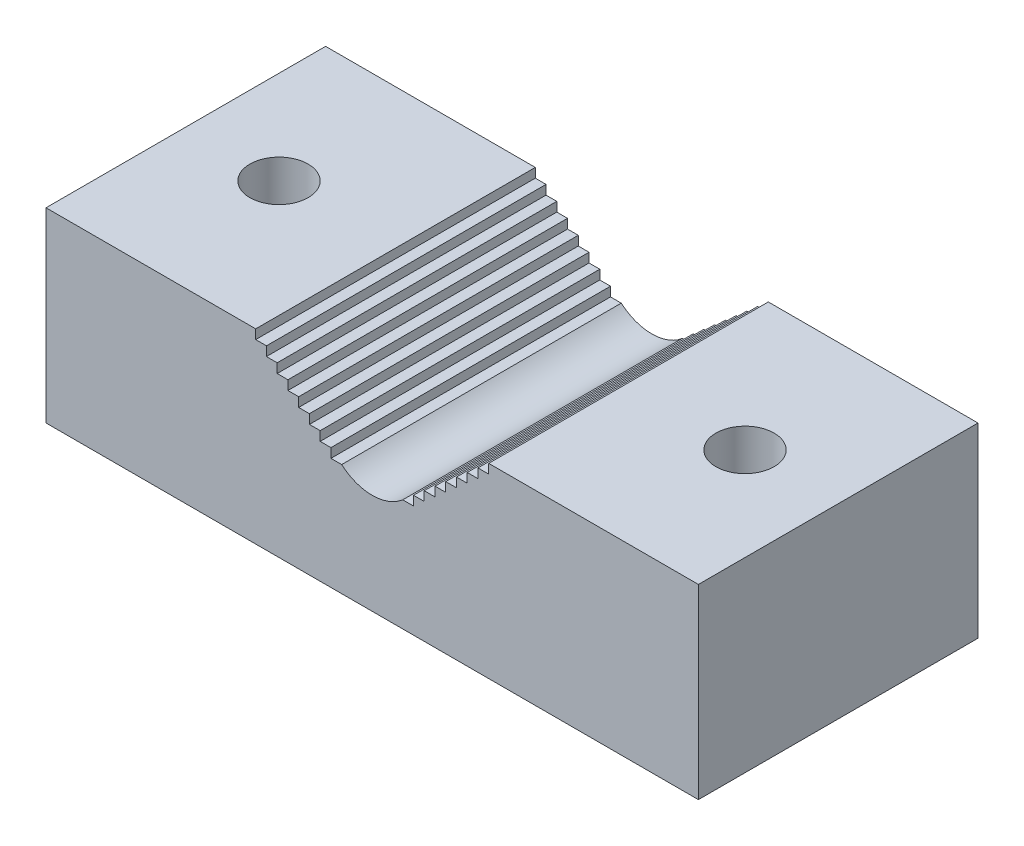
SolidWorks part; units mm, degrees
material "6061-T6 (SS)"
ref_plane "Front Plane" through (0, 0, 0) normal (0, 0, 1) x (1, 0, 0)
ref_plane "Top Plane" through (0, 0, 0) normal (0, 1, 0) x (1, 0, 0)
ref_plane "Right Plane" through (0, 0, 0) normal (1, 0, 0) x (0, 0, -1)
sketch "Sketch1" plane through (0, 0, 0) normal (0, 0, 1) x (1, 0, 0)
  line L0 (-44.45, 0) -> (44.45, 0)
  line L1 (44.45, 0) -> (44.45, 25.4)
  line L2 (44.45, 25.4) -> (-44.45, 25.4)
  line L3 (-44.45, 25.4) -> (-44.45, 0)
  point P3 (0, 0)
  dimension "D1" = 25.4
  dimension "D2" = 88.9
extrude "Boss-Extrude1" add sketch "Sketch1" against normal blind 38.1
sketch "Sketch2" plane through (0, 0, 0) normal (0, 0, 1) x (1, 0, 0)
  line L0 (-15.875, 25.4) -> (-4.1606, 15.24) construction
  line L1 (-15.875, 25.4) -> (0, 25.4)
  line L2 (44.45, 25.4) -> (-44.45, 25.4) construction
  line L3 (15.875, 25.4) -> (4.1606, 15.24) construction
  line L4 (15.875, 25.4) -> (0, 25.4)
  line L5 (-15.875, 25.4) -> (-15.875, 24.13)
  line L6 (-15.875, 24.13) -> (-14.4107, 24.13)
  line L7 (-14.4107, 24.13) -> (-14.4107, 22.86)
  line L8 (-14.4107, 22.86) -> (-12.9464, 22.86)
  line L9 (-12.9464, 22.86) -> (-12.9464, 21.59)
  line L10 (-12.9464, 21.59) -> (-11.4821, 21.59)
  line L11 (-11.4821, 21.59) -> (-11.4821, 20.32)
  line L12 (-11.4821, 20.32) -> (-10.0178, 20.32)
  line L13 (-10.0178, 20.32) -> (-10.0178, 19.05)
  line L14 (-10.0178, 19.05) -> (-8.5535, 19.05)
  line L15 (-8.5535, 19.05) -> (-8.5535, 17.78)
  line L16 (-8.5535, 17.78) -> (-7.0892, 17.78)
  line L17 (-7.0892, 17.78) -> (-7.0892, 16.51)
  line L18 (-7.0892, 16.51) -> (-5.6249, 16.51)
  line L19 (-5.6249, 16.51) -> (-5.6249, 15.24)
  line L20 (-5.6249, 15.24) -> (-4.1606, 15.24)
  line L21 (0, 25.4) -> (0, 0) construction
  line L24 (5.6249, 15.24) -> (4.1606, 15.24)
  line L25 (5.6249, 16.51) -> (5.6249, 15.24)
  line L26 (7.0892, 16.51) -> (5.6249, 16.51)
  line L27 (7.0892, 17.78) -> (7.0892, 16.51)
  line L28 (8.5535, 17.78) -> (7.0892, 17.78)
  line L29 (8.5535, 19.05) -> (8.5535, 17.78)
  line L30 (10.0178, 19.05) -> (8.5535, 19.05)
  line L31 (10.0178, 20.32) -> (10.0178, 19.05)
  line L32 (11.4821, 20.32) -> (10.0178, 20.32)
  line L33 (11.4821, 21.59) -> (11.4821, 20.32)
  line L34 (12.9464, 21.59) -> (11.4821, 21.59)
  line L35 (12.9464, 22.86) -> (12.9464, 21.59)
  line L36 (14.4107, 22.86) -> (12.9464, 22.86)
  line L37 (14.4107, 24.13) -> (14.4107, 22.86)
  line L38 (15.875, 24.13) -> (14.4107, 24.13)
  line L39 (15.875, 25.4) -> (15.875, 24.13)
  arc A0 (4.1606, 15.24) -> (-4.1606, 15.24) centre (0, 20.0371) cw
  point P7 (0, 25.4)
  dimension "D1" = 6.35
  dimension "D2" = 31.75
  dimension "D4" = 1.27
extrude "Cut-Extrude1" cut sketch "Sketch2" against normal up to next
sketch "Sketch3" plane through (0, 0, 0) normal (0, 0, 1) x (1, 0, 0)
  circle A0 centre (0, 24.151) radius 14.2875
  dimension "D1" = 28.575
hole_wizard "3/8-16 Tapped Hole1" positions "Sketch6" profile "Sketch5" tap size "3/8-16" standard "ANSI Inch" end condition through all
sketch "Sketch6" plane through (0, 25.4, 0) normal (0, 1, 0) x (1, 0, 0)
  line L1 (-44.45, 38.1) -> (-44.45, 0) construction
  line L3 (44.45, 38.1) -> (44.45, 0) construction
  point P0 (-31.75, 19.05)
  point P2 (31.75, 19.05)
  point P10 (-44.45, 19.05)
  point P16 (44.45, 19.05)
  dimension "D1" = 12.7
  dimension "D2" = 12.7
sketch "Sketch5" plane through (-31.75, 25.4, -19.05) normal (1, 0, 0) x (0, 0, 1)
  line L0 (0, 0) -> (0, 25.4)
  line L1 (0, 25.4) -> (3.9687, 25.4)
  line L2 (3.9687, 25.4) -> (3.9687, 0)
  line L5 (3.9687, 0) -> (0, 0)
  line L11 (0, -6.35) -> (0, 107.95) construction
  dimension "Thread Major Dia." = 7.9375
  dimension "Thru Tap Drill Depth" = 25.4
hole_wizard "1/4-20 Tapped Hole1" positions "Sketch7" profile "Sketch8" tap size "1/4-20" standard "ANSI Inch"
sketch "Sketch7" plane through (0, 0, 0) normal (0, -1, 0) x (-1, 0, 0)
  line L0 (0, 38.1) -> (0, 0) construction
  line L1 (44.45, 38.1) -> (-44.45, 38.1) construction
  line L2 (44.45, 38.1) -> (44.45, 0) construction
  point P0 (-20.32, 19.05)
  point P2 (20.32, 19.05)
  point P15 (44.45, 19.05)
  dimension "D1" = 20.32
  dimension "D2" = 20.32
sketch "Sketch8" plane through (20.32, 0, -19.05) normal (1, 0, 0) x (0, 0, -1)
  line L0 (0, 0) -> (0, 18.0438)
  line L1 (0, 18.0438) -> (2.5527, 16.51)
  line L2 (2.5527, 16.51) -> (2.5527, 0)
  line L5 (2.5527, 0) -> (0, 0)
  line L10 (0, 18.0438) -> (-2.5527, 16.51) construction
  line L11 (0, -6.35) -> (0, 107.95) construction
  dimension "Tap Drill Dia." = 5.1054
  dimension "Tap Drill Depth" = 16.51
  dimension "Drill Angle" = 118
cosmetic thread "Hole Thread1" parameters "D1"=12.7, "D2"=6.35
cosmetic thread "Hole Thread2" parameters "D1"=12.7, "D2"=6.35
